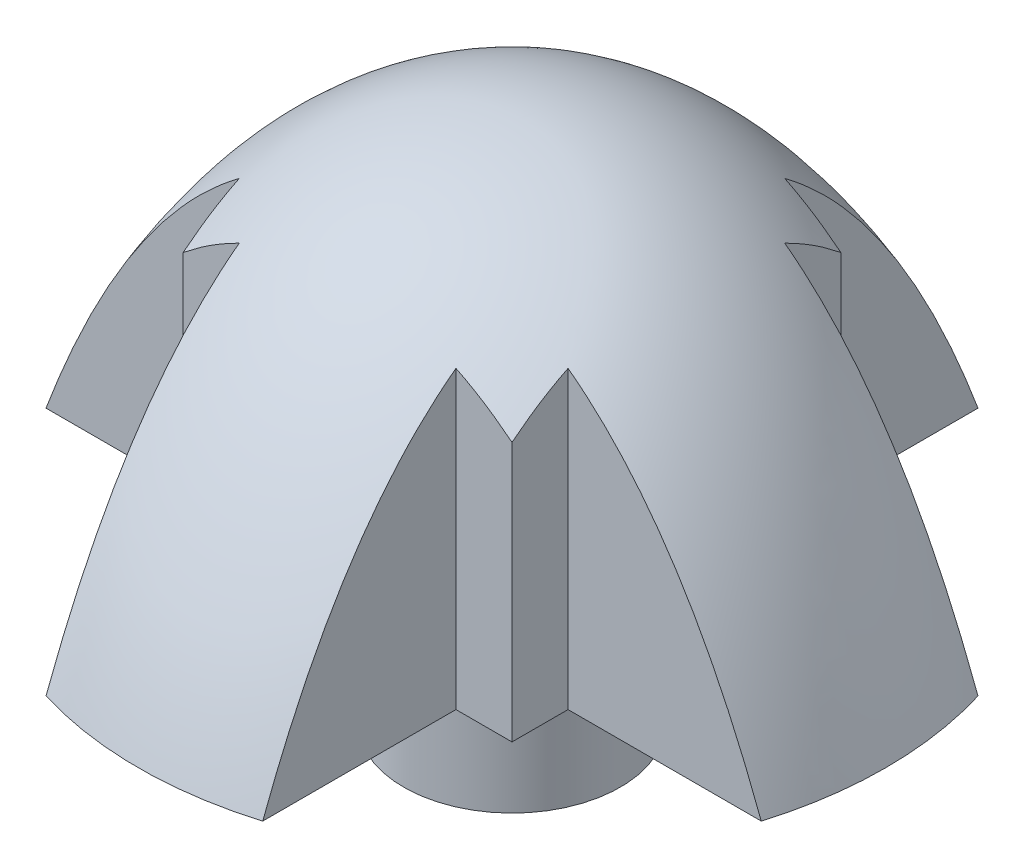
SolidWorks part; units mm, degrees
ref_plane "Front Plane" through (0, 0, 0) normal (0, 0, 1) x (1, 0, 0)
ref_plane "Top Plane" through (0, 0, 0) normal (0, 1, 0) x (1, 0, 0)
ref_plane "Right Plane" through (0, 0, 0) normal (1, 0, 0) x (0, 0, -1)
sketch "Sketch3" plane through (0, 0, 0) normal (0, 0, 1) x (1, 0, 0)
  line L2 (0, 5) -> (0, 0)
  line L4 (5, 0) -> (0, 0)
  line L5 (0, 5) -> (-1.1298, 5) construction
  line L6 (0, 4.6) -> (-1.1298, 4.6) construction
  line L8 (0, 0) -> (1.45, 0)
  line L9 (0, 0) -> (2.5, 0)
  line L10 (0, 0) -> (0, 0.5)
  line L13 (0, 0) -> (0, -2)
  line L14 (0, -2) -> (1.45, -2)
  line L15 (1.45, 0) -> (1.45, -2)
  spline S0 degree 2 poles (5, 0) (3.2016, 5) (0, 5) knots 0 0 0 1 1 1
  point P3 (0, 4.6)
  dimension "D1" = 5
  dimension "D2" = 5
  dimension "D3" = 1.45
  dimension "D4" = 0.4
  dimension "D5" = 2
revolve "Revolve1" add sketch "Sketch3" angle 360 about L2
sketch "Sketch5" plane through (0, 0, 0) normal (0, -1, 0) x (1, 0, 0)
  line L0 (-4.7851, -1.45) -> (4.7851, -1.45) construction
  line L1 (4.7851, 1.45) -> (-4.7851, 1.45) construction
  line L2 (1.45, 4.7851) -> (1.45, -4.7851) construction
  line L3 (-1.45, -4.7851) -> (-1.45, 4.7851) construction
  line L5 (2.2, 2.2) -> (-2.2, 2.2)
  line L6 (2.2, 2.2) -> (2.2, -2.2)
  line L7 (2.2, -2.2) -> (-2.2, -2.2)
  line L8 (-2.2, 2.2) -> (-2.2, -2.2)
  line L9 (2.2, 2.2) -> (-2.2, -2.2) construction
  line L10 (2.2, -2.2) -> (-2.2, 2.2) construction
  line L11 (-4.7851, -1.45) -> (-1.45, -1.45)
  line L12 (-4.7851, -1.45) -> (-4.7851, -4.7851)
  line L13 (-4.7851, -4.7851) -> (-1.45, -4.7851)
  line L14 (-1.45, -1.45) -> (-1.45, -4.7851)
  line L15 (-4.7851, 1.45) -> (-1.45, 1.45)
  line L16 (-4.7851, 1.45) -> (-4.7851, 4.7851)
  line L17 (-4.7851, 4.7851) -> (-1.45, 4.7851)
  line L18 (-1.45, 1.45) -> (-1.45, 4.7851)
  line L19 (1.45, 4.7851) -> (4.7851, 4.7851)
  line L20 (1.45, 4.7851) -> (1.45, 1.45)
  line L21 (1.45, 1.45) -> (4.7851, 1.45)
  line L22 (4.7851, 4.7851) -> (4.7851, 1.45)
  line L23 (1.45, -4.7851) -> (4.7851, -4.7851)
  line L24 (1.45, -4.7851) -> (1.45, -1.45)
  line L25 (1.45, -1.45) -> (4.7851, -1.45)
  line L26 (4.7851, -4.7851) -> (4.7851, -1.45)
  circle A0 centre (0, 0) radius 5 construction
  circle A2 centre (0, 0) radius 1.45
  circle A3 centre (0, 0) radius 1.45
  circle M11 centre (0, 0) radius 5
  dimension "D2" = 0.75
  dimension "D1" = 0
extrude "Cut-Extrude1" cut sketch "Sketch5" against normal up to next contours L5 L18 L15 L8 M11 | L6 L21 L20 L5 M11 | L25 L6 L7 L24 M11 | L14 L7 L8 L11 M11
